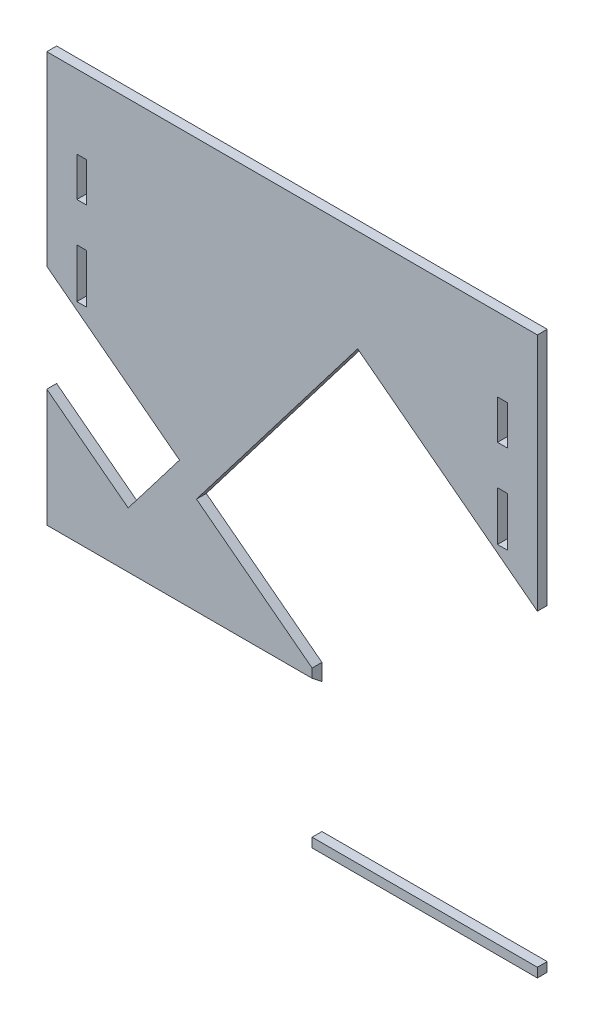
SolidWorks part; units mm, degrees
ref_plane "Front Plane" through (0, 0, 0) normal (0, 0, 1) x (1, 0, 0)
ref_plane "Top Plane" through (0, 0, 0) normal (0, 1, 0) x (1, 0, 0)
ref_plane "Right Plane" through (0, 0, 0) normal (1, 0, 0) x (0, 0, -1)
sketch "Sketch1" plane through (0, 0, 0) normal (0, 0, 1) x (1, 0, 0)
  line L0 (124.8, 0) -> (124.8, -283.36) construction
  line L1 (0, 0) -> (249.6, 0)
  line L2 (0, 0) -> (0, -283.36)
  line L3 (0, -283.36) -> (249.6, -283.36)
  line L4 (249.6, 0) -> (249.6, -283.36)
  dimension "D1" = 249.6
  dimension "D2" = 283.36
extrude "Boss-Extrude1" add sketch "Sketch1" along normal blind 5
sketch "Sketch2" plane through (0, 0, 5) normal (0, 0, 1) x (1, 0, 0)
  line L0 (-12.0438, -116.1701) -> (14.8299, 12.0438) construction
  line L1 (357.917, -193.7139) -> (384.7906, -65.5) construction
  line L2 (-12.0438, -116.1701) -> (357.917, -193.7139) construction
  line L3 (28.6688, 50.2813) -> (25.735, 46.2325) construction
  line L4 (25.735, 46.2325) -> (79.8591, 7.0134) construction
  line L5 (89.8056, 5.9807) -> (28.6688, 50.2813) construction
  line L6 (14.8299, 12.0438) -> (384.7906, -65.5) construction
  line L7 (14.2144, 9.1076) -> (384.1752, -68.4362) construction
  line L8 (-11.4283, -113.2339) -> (358.5324, -190.7777) construction
  line L9 (28.6688, 50.2813) -> (31.6026, 54.33) construction
  line L10 (31.6026, 54.33) -> (85.7267, 15.111) construction
  line L11 (236.1909, -165.1349) -> (261.8337, -42.7934) construction
  line L12 (126.6708, -78.3214) -> (249.0123, -103.9642) construction
  line L13 (113.8494, -139.4922) -> (139.4922, -17.1506) construction
  line L14 (249.6, 0) -> (0, 0) construction
  line L15 (0, 0) -> (0, -283.36) construction
  circle A0 centre (65.5, -65.5) radius 62.5 construction
  circle A1 centre (310.183, -116.7856) radius 62.5 construction
  circle A2 centre (65.5, -65.5) radius 65.5 construction
  circle A3 centre (187.8415, -91.1428) radius 62.5 construction
  circle A4 centre (89.8056, 5.9807) radius 75.5 construction
  circle A5 centre (89.8056, 5.9807) radius 2.5 construction
  circle A6 centre (69.5617, 20.6497) radius 1.5 construction
  arc A7 (79.8591, 7.0134) -> (85.7267, 15.111) centre (89.8056, 5.9807) ccw construction
  dimension "D1" = 125
  dimension "D2" = 125
  dimension "D3" = 5
  dimension "D6" = 3
  dimension "D7" = 10
  dimension "D10" = 125
  dimension "D8" = 3
  dimension "D4" = 5
  dimension "D5" = 25
  dimension "D9" = 5
sketch "Sketch3" plane through (0, -131.9697, 103.1061) normal (0, 0.788, -0.6157) x (1, 0, 0)
  line L0 (135, 268.1918) -> (135, 58.3128) construction
  line L1 (135, 218.6086) -> (0, 218.6086)
  line L2 (135, 218.6086) -> (135, -11.4057)
  line L3 (135, -11.4057) -> (0, -11.4057)
  line L4 (0, 218.6086) -> (0, -11.4057)
  line L5 (0, 268.1918) -> (0, 58.3128) construction
extrude "Cut-Extrude1" cut sketch "Sketch3" against normal blind 193
sketch "Sketch4" plane through (0, 0, 5) normal (0, 0, 1) x (1, 0, 0)
  line L1 (214.957, -95.2783) -> (249.6, -121.7672)
  line L3 (249.6, -121.7672) -> (249.6, -278.6121)
  line L4 (54.8789, 27.1214) -> (359.1299, -205.5164) construction
  line L5 (135, -204.0831) -> (76.1492, -159.0843)
  line L6 (-27.1214, -80.1211) -> (277.1296, -312.7589) construction
  line L7 (76.1492, -159.0843) -> (158.1494, -51.8418)
  line L8 (79.1862, -155.1124) -> (155.1124, -55.8138) construction
  line L9 (158.1494, -51.8418) -> (214.957, -95.2783)
  line L10 (135, -340.9) -> (135, 0) construction
  line L11 (135, -204.0831) -> (135, -278.6121)
  line L12 (135, -278.6121) -> (249.6, -278.6121)
  line L13 (264.875, -278.6121) -> (5.125, -278.6121) construction
  line L14 (249.6, -158.4475) -> (249.6, 0) construction
extrude "Cut-Extrude2" cut sketch "Sketch4" against normal through all
sketch "Sketch5" plane through (0, 0, 5) normal (0, 0, 1) x (1, 0, 0)
  line L0 (0, -94.5647) -> (67.5231, -146.1945)
  line L1 (0, -94.5647) -> (-26.1186, -128.7234)
  line L2 (67.5231, -146.1945) -> (41.4045, -180.3532)
  line L3 (-26.1186, -128.7234) -> (41.4045, -180.3532)
  line L4 (0, 0) -> (0, -208.6186) construction
  line L5 (-24.0843, -76.1492) -> (280.1666, -308.787) construction
  dimension "D1" = 85
  dimension "D2" = 43
extrude "Cut-Extrude3" cut sketch "Sketch5" against normal through all
sketch "Sketch6" plane through (0, 0, 5) normal (0, 0, 1) x (1, 0, 0)
  circle A0 centre (763.4957, -447.3227) radius 2.1
  circle A1 centre (787.8071, -441.4955) radius 2.1
  circle A2 centre (793.6343, -465.8069) radius 2.1
  circle A3 centre (769.323, -471.6341) radius 2.1
  circle A4 centre (797.7134, -482.8249) radius 2.1
  circle A5 centre (773.402, -488.6521) radius 2.1
  circle A6 centre (763.4957, -447.3227) radius 2.1 construction
  circle A7 centre (769.323, -471.6341) radius 2.1 construction
  circle A8 centre (787.8071, -441.4955) radius 2.1 construction
  circle A9 centre (793.6343, -465.8069) radius 2.1 construction
  circle A10 centre (797.7134, -482.8249) radius 2.1 construction
  circle A11 centre (773.402, -488.6521) radius 2.1 construction
  circle A12 centre (784.3923, -480.8762) radius 4
  circle A13 centre (778.565, -456.5648) radius 4
  circle A14 centre (784.3923, -480.8762) radius 4 construction
  circle A15 centre (778.565, -456.5648) radius 4 construction
extrude "Cut-Extrude4" cut sketch "Sketch6" against normal through all
sketch "Sketch7" plane through (0, 0, 5) normal (0, 0, 1) x (1, 0, 0)
  line L0 (124.8, -7.0792) -> (124.8, -189.5476) construction
  line L1 (15.2882, -37.4779) -> (20.2882, -37.4779)
  line L2 (15.2882, -37.4779) -> (15.2882, -57.4779)
  line L3 (15.2882, -57.4779) -> (20.2882, -57.4779)
  line L4 (20.2882, -37.4779) -> (20.2882, -57.4779)
  line L5 (229.3118, -37.4779) -> (234.3118, -37.4779)
  line L6 (229.3118, -37.4779) -> (229.3118, -57.4779)
  line L7 (229.3118, -57.4779) -> (234.3118, -57.4779)
  line L8 (234.3118, -37.4779) -> (234.3118, -57.4779)
  line L9 (15.2882, -77.4779) -> (20.2882, -77.4779)
  line L10 (15.2882, -77.4779) -> (15.2882, -102.4779)
  line L11 (15.2882, -102.4779) -> (20.2882, -102.4779)
  line L12 (20.2882, -77.4779) -> (20.2882, -102.4779)
  line L13 (229.3118, -77.4779) -> (234.3118, -77.4779)
  line L14 (229.3118, -77.4779) -> (229.3118, -102.4779)
  line L15 (229.3118, -102.4779) -> (234.3118, -102.4779)
  line L16 (234.3118, -77.4779) -> (234.3118, -102.4779)
  line L17 (17.7882, -37.4779) -> (17.7882, -160.2371) construction
  line L18 (231.8118, -37.4779) -> (231.8118, -160.4946) construction
  line L20 (249.6, -121.7672) -> (249.6, 0) construction
  line L21 (0, 0) -> (0, -94.5647) construction
  line L22 (67.5231, -146.1945) -> (0, -94.5647) construction
  line L23 (249.6, -121.7672) -> (158.1494, -51.8418) construction
  dimension "D1" = 5
  dimension "D2" = 20
  dimension "D3" = 5
  dimension "D4" = 20
  dimension "D5" = 5
  dimension "D6" = 25
  dimension "D7" = 5
  dimension "D8" = 25
  dimension "D9" = 20
  dimension "D10" = 20
  dimension "D11" = 3
  dimension "D12" = 3
extrude "Cut-Extrude5" cut sketch "Sketch7" against normal through all
